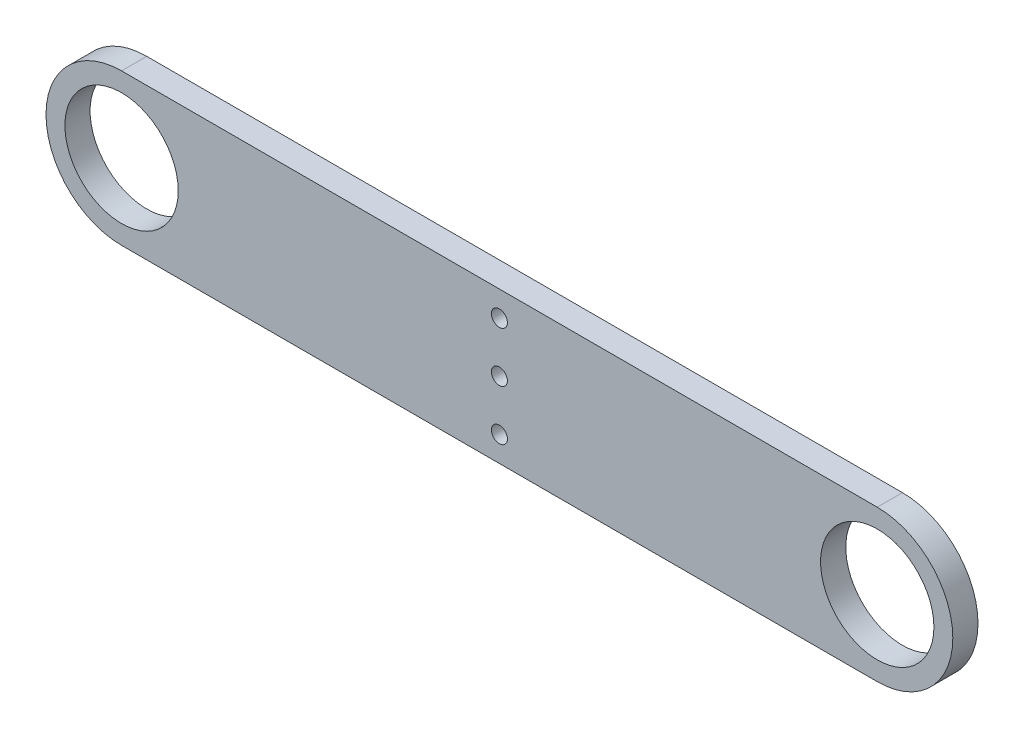
SolidWorks part; units mm, degrees
ref_plane "Front Plane" through (0, 0, 0) normal (0, 0, 1) x (1, 0, 0)
ref_plane "Top Plane" through (0, 0, 0) normal (0, 1, 0) x (1, 0, 0)
ref_plane "Right Plane" through (0, 0, 0) normal (1, 0, 0) x (0, 0, -1)
sketch "Sketch1" plane through (0, 0, 0) normal (0, 0, 1) x (1, 0, 0)
  line L0 (0, -25.4) -> (0, 25.4) construction
  line L1 (95.25, 0) -> (-95.25, 0)
  line L2 (-95.25, 19.05) -> (95.25, 19.05)
  line L3 (95.25, -19.05) -> (-95.25, -19.05)
  circle A0 centre (-95.25, 0) radius 14.2875
  circle A1 centre (95.25, 0) radius 14.2875
  arc A2 (-95.25, 19.05) -> (-95.25, -19.05) centre (-95.25, 0) ccw
  arc A3 (95.25, 19.05) -> (95.25, -19.05) centre (95.25, 0) cw
  circle A4 centre (0, 12.7) radius 2.0193
  circle A5 centre (0, 0) radius 2.0193
  circle A6 centre (0, -12.7) radius 2.0193
  point P4 (0, 0)
  point P8 (0, 0)
  dimension "D3" = 28.575
  dimension "D4" = 28.575
  dimension "D5" = 19.05
  dimension "D7" = 4.0386
  dimension "D1" = 50.8
  dimension "D2" = 190.5
  dimension "D6" = 12.7
  dimension "D8" = 3
extrude "Boss-Extrude1" add sketch "Sketch1" along normal blind 6.35
